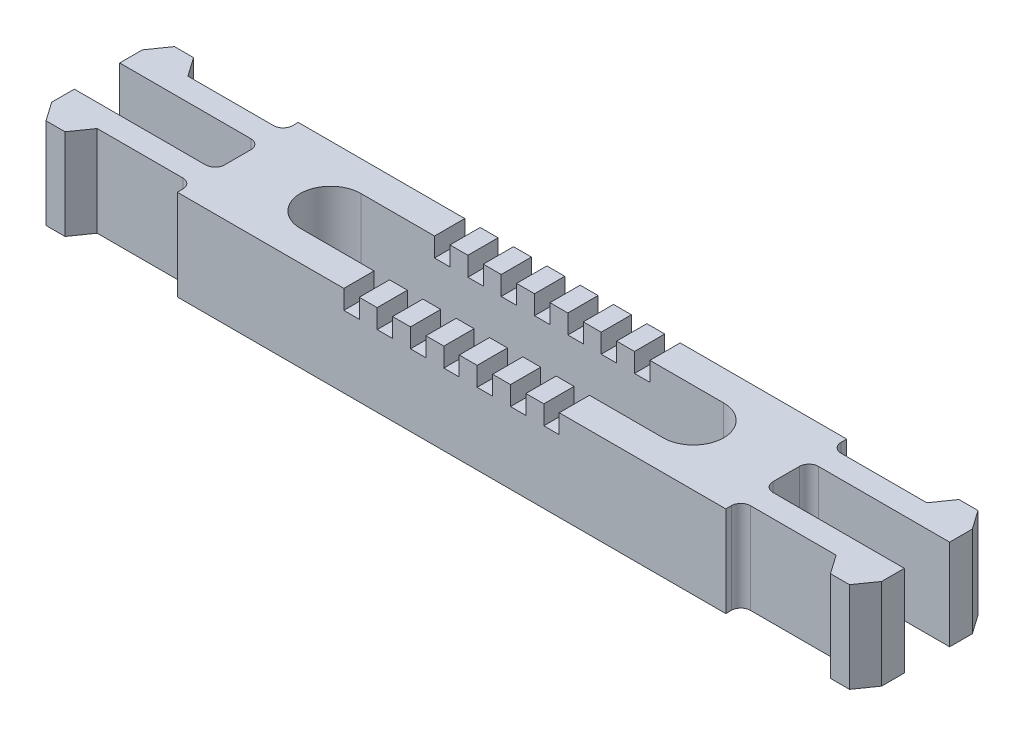
SolidWorks part; units mm, degrees
ref_plane "Front" through (0, 0, 0) normal (0, 0, 1) x (1, 0, 0)
ref_plane "Top" through (0, 0, 0) normal (0, 1, 0) x (1, 0, 0)
ref_plane "Right" through (0, 0, 0) normal (1, 0, 0) x (0, 0, -1)
sketch "Sketch1" plane through (0, 0, 0) normal (0, 1, 0) x (1, 0, 0)
  line L1 (-28.8, 6.35) -> (28.8, 6.35)
  line L2 (-28.8, 6.35) -> (-28.8, -6.35)
  line L3 (-28.8, -6.35) -> (28.8, -6.35)
  line L4 (28.8, 6.35) -> (28.8, -6.35)
  line L5 (-28.8, 6.35) -> (28.8, -6.35) construction
  line L6 (-28.8, -6.35) -> (28.8, 6.35) construction
  line L12 (-22.7682, 0) -> (21.9581, 0) construction
  line L13 (0, 9.9214) -> (0, -9.6014) construction
  point P0 (0, 0)
extrude "Boss-Extrude1" add sketch "Sketch1" along normal blind 9.525
sketch "Sketch2" plane through (0, 9.525, 0) normal (0, 1, 0) x (1, 0, 0)
  line L0 (-28.8, 4.7625) -> (-38.8, 4.7625)
  line L1 (-28.8, 6.35) -> (-28.8, -6.35) construction
  line L2 (-38.8, 4.7625) -> (-40.1895, 6.7469)
  line L3 (-40.1895, 6.7469) -> (-42.1895, 6.7469)
  line L4 (-42.1895, 6.7469) -> (-43.5789, 4.7625)
  line L5 (-43.5789, 4.7625) -> (-43.5789, 2.3812)
  line L6 (-43.5789, 2.3812) -> (-28.8, 2.3812)
  line L7 (-28.8, 2.3812) -> (-28.8, 4.7625)
  line L8 (28.8, 6.35) -> (-28.8, 6.35) construction
  dimension "D1" = 10
  dimension "D2" = 125
  dimension "D3" = 2.3813
  dimension "D4" = 1.5875
  dimension "D5" = 0.3969
  dimension "D6" = 2
extrude "Boss-Extrude2" add sketch "Sketch2" against normal up to surface (9.525 mm away) up to face at (0, 0, 0)
mirror "Mirror1" about plane through (0, 0, 0) normal (1, 0, 0) of "Boss-Extrude2"
mirror "Mirror2" about plane through (0, 0, 0) normal (0, 0, 1) of "Boss-Extrude2", "Mirror1"
fillet "Fillet1" radius 1 8 edges at (28.8, 4.7625, 4.7625) (28.8, 4.7625, 2.3812) (28.8, 4.7625, -2.3812) (28.8, 4.7625, -4.7625) (-28.8, 4.7625, 2.3812) (-28.8, 4.7625, 4.7625) (-28.8, 4.7625, -4.7625) (-28.8, 4.7625, -2.3812)
sketch "Sketch4" plane through (0, 9.525, 0) normal (0, 1, 0) x (1, 0, 0)
  line L0 (-19.05, 0) -> (19.05, 0) construction
  line L1 (-19.05, 3.175) -> (19.05, 3.175)
  line L2 (-19.05, -3.175) -> (19.05, -3.175)
  arc A0 (-19.05, 3.175) -> (-19.05, -3.175) centre (-19.05, 0) ccw
  arc A1 (19.05, -3.175) -> (19.05, 3.175) centre (19.05, 0) ccw
  point P2 (0, 0)
  dimension "D1" = 6.35
  dimension "D2" = 38.1
extrude "Cut-Extrude1" cut sketch "Sketch4" against normal through all
sketch "Sketch3" plane through (0, 9.525, 0) normal (0, 1, 0) x (1, 0, 0)
  line L0 (-28.8, -6.35) -> (28.8, -6.35) construction
  line L1 (-0.81, 6.35) -> (0.81, 6.35)
  line L2 (-0.81, 6.35) -> (-0.81, -6.35)
  line L3 (-0.81, -6.35) -> (0.81, -6.35)
  line L4 (0.81, 6.35) -> (0.81, -6.35)
  line L5 (-0.81, 6.35) -> (0.81, -6.35) construction
  line L6 (-0.81, -6.35) -> (0.81, 6.35) construction
  point P0 (0, 0)
  dimension "D1" = 1.62
extrude "Cut-Extrude2" cut sketch "Sketch3" against normal blind 2
pattern_linear "LPattern1" count 4 spacing 3.5 along (-1, 0, 0) count 4 spacing 3.5 along (1, 0, 0) of "Cut-Extrude2"
sketch "Sketch5" plane through (0, 0, 6.35) normal (0, 0, 1) x (1, 0, 0)
  line L0 (-29.8, 0) -> (-29.8, 9.525) construction
  circle A0 centre (-24.257, 4.7625) radius 1.5875
  circle A1 centre (24.257, 4.7625) radius 1.5875
  point P4 (-29.8, 4.7625)
  dimension "D1" = 3.175
  dimension "D2" = 48.514
  dimension "D3" = 24.257
extrude "Boss-Extrude3" [suppressed] add sketch "Sketch5" along normal blind 6.35
mirror "Mirror4" [suppressed] about plane through (0, 0, 0) normal (0, 0, 1)
